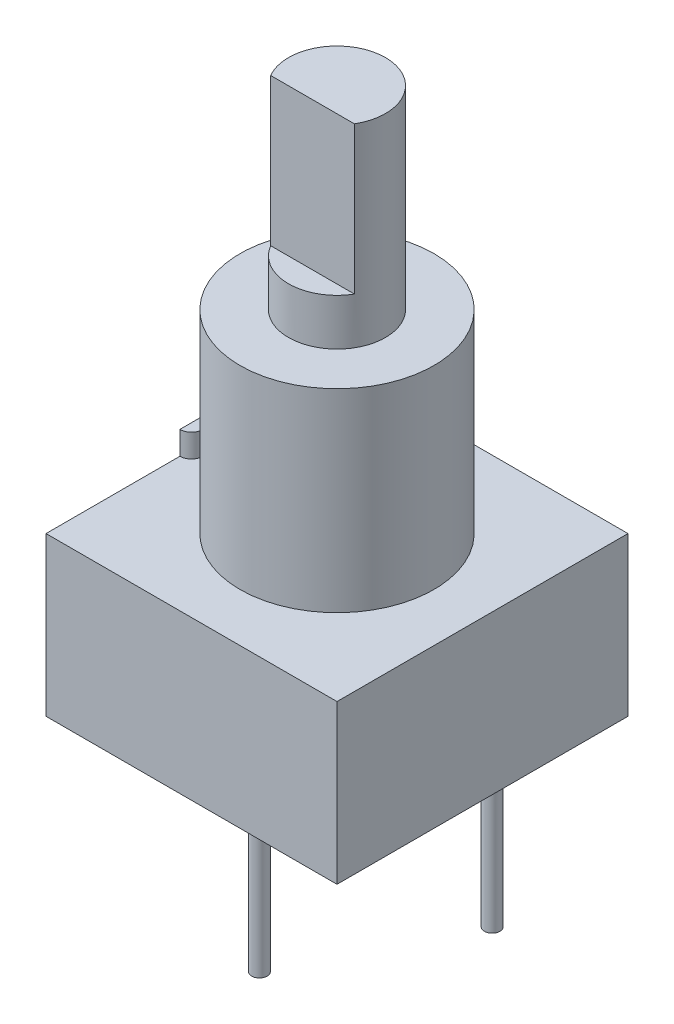
SolidWorks part; units mm, degrees
ref_plane "Front Plane" through (0, 0, 0) normal (0, 0, 1) x (1, 0, 0)
ref_plane "Top Plane" through (0, 0, 0) normal (0, 1, 0) x (1, 0, 0)
ref_plane "Right Plane" through (0, 0, 0) normal (1, 0, 0) x (0, 0, -1)
sketch "Sketch1" plane through (0, 0, 0) normal (0, 1, 0) x (1, 0, 0)
  line L1 (4.7625, -4.7625) -> (-4.7625, -4.7625)
  line L2 (4.7625, -4.7625) -> (4.7625, 4.7625)
  line L3 (4.7625, 4.7625) -> (-4.7625, 4.7625)
  line L4 (-4.7625, -4.7625) -> (-4.7625, 4.7625)
  line L5 (4.7625, -4.7625) -> (-4.7625, 4.7625) construction
  line L6 (4.7625, 4.7625) -> (-4.7625, -4.7625) construction
  point P0 (0, 0)
  dimension "D1" = 9.525
extrude "Boss-Extrude1" add sketch "Sketch1" against normal blind 5.1816
sketch "Sketch2" plane through (0, 0, 0) normal (0, 1, 0) x (1, 0, 0)
  circle A0 centre (0, 0) radius 3.175
  dimension "D1" = 6.35
extrude "Boss-Extrude2" add sketch "Sketch2" along normal blind 6.35
sketch "Sketch3" plane through (0, 0, 0) normal (0, 1, 0) x (1, 0, 0)
  line L0 (-4.7625, 4.7625) -> (-4.7625, -4.7625) construction
  line L1 (-4.7625, 0.381) -> (-4.7625, -0.381)
  arc A0 (-4.7625, -0.381) -> (-4.7625, 0.381) centre (-4.7625, 0) ccw
  dimension "D1" = 0.762
extrude "Boss-Extrude3" add sketch "Sketch3" along normal blind 0.762
sketch "Sketch4" plane through (0, 6.35, 0) normal (0, 1, 0) x (1, 0, 0)
  circle A0 centre (0, 0) radius 1.5875
  dimension "D1" = 3.175
extrude "Boss-Extrude4" add sketch "Sketch4" along normal offset from surface (6.35 mm away) 12.7 contours A0 up to face at (0, 0, 3.175) offset beyond the face yes
sketch "Sketch5" plane through (0, 12.7, 0) normal (0, 1, 0) x (1, 0, 0)
  line L0 (-1.3711, -0.8001) -> (1.3711, -0.8001)
  circle A1 centre (0, 0) radius 1.5875
  arc A2 (-1.3711, -0.8001) -> (1.3711, -0.8001) centre (0, 0) ccw
  point P5 (0, 1.5875)
  dimension "D2" = 2.3876
  dimension "D1" = 0
extrude "Cut-Extrude1" cut sketch "Sketch5" against normal blind 4.826
sketch "Sketch6" plane through (0, -5.1816, 0) normal (0, -1, 0) x (1, 0, 0)
  circle A0 centre (0, 2.54) radius 0.254
  circle A1 centre (-2.54, -2.54) radius 0.254
  circle A2 centre (2.54, -2.54) radius 0.254
  dimension "D1" = 0.508
  dimension "D4" = 5.08
  dimension "D2" = 2.54
  dimension "D3" = 2.54
  dimension "D5" = 2.54
extrude "Boss-Extrude5" add sketch "Sketch6" along normal blind 5.969
